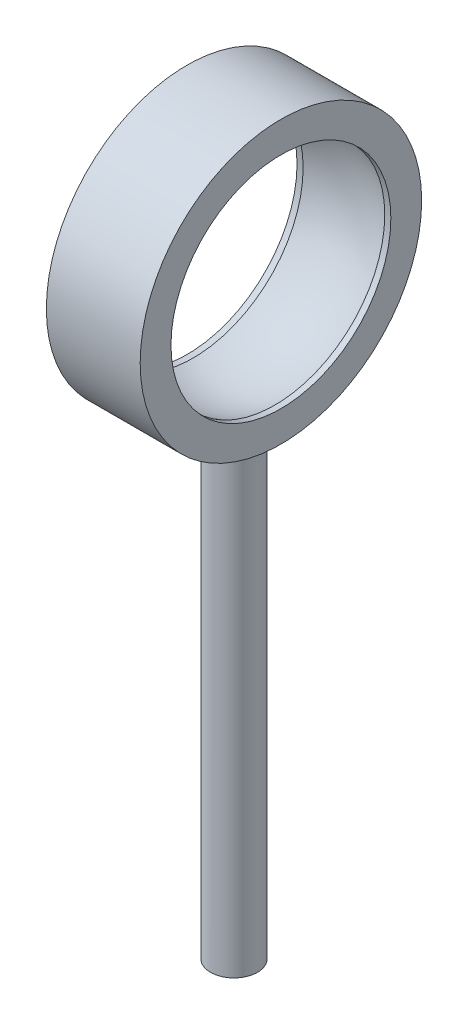
SolidWorks part; units mm, degrees
ref_plane "Front Plane" through (0, 0, 0) normal (0, 0, 1) x (1, 0, 0)
ref_plane "Top Plane" through (0, 0, 0) normal (0, 1, 0) x (1, 0, 0)
ref_plane "Right Plane" through (0, 0, 0) normal (1, 0, 0) x (0, 0, -1)
sketch "Sketch1" plane through (0, 0, 0) normal (0, 0, 1) x (1, 0, 0)
  line L0 (-10.16, 0) -> (12.9754, 0) construction
  line L2 (2.54, 7.62) -> (-2.54, 7.62)
  line L3 (2.54, 7.62) -> (2.54, 5.9531)
  line L5 (-2.54, 7.62) -> (-2.54, 5.9531)
  line L6 (2.54, 7.62) -> (-2.54, 5.9531) construction
  line L7 (2.54, 5.9531) -> (-2.54, 7.62) construction
  line L8 (-2.54, 5.9531) -> (-2.2097, 5.9531)
  line L9 (2.2097, 5.9531) -> (2.54, 5.9531)
  arc A0 (-2.2097, 5.9531) -> (2.2097, 5.9531) centre (0, 0) cw
  point P3 (0, 6.7866)
  point P8 (0, 7.62)
  dimension "D4" = 6.35
  dimension "D1" = 5.08
  dimension "D2" = 7.62
  dimension "D3" = 0.3303
revolve "Revolve1" add sketch "Sketch1" angle 360 about L0
sketch "Sketch2" plane through (0, 0, 0) normal (1, 0, 0) x (0, 0, -1)
  line L1 (0, 0) -> (0, -62.6561) construction
  line L2 (1.27, -7.5134) -> (1.27, -33.02)
  line L4 (0, -33.02) -> (0, -7.62)
  line L5 (0, -33.02) -> (1.27, -33.02)
  circle A4 centre (0, 0) radius 7.62 construction
  arc A5 (0, -7.62) -> (1.27, -7.5134) centre (0, 0) ccw
  dimension "D1" = 25.4
  dimension "D2" = 1.27
revolve "Revolve2" add sketch "Sketch2" angle 360 about L4
